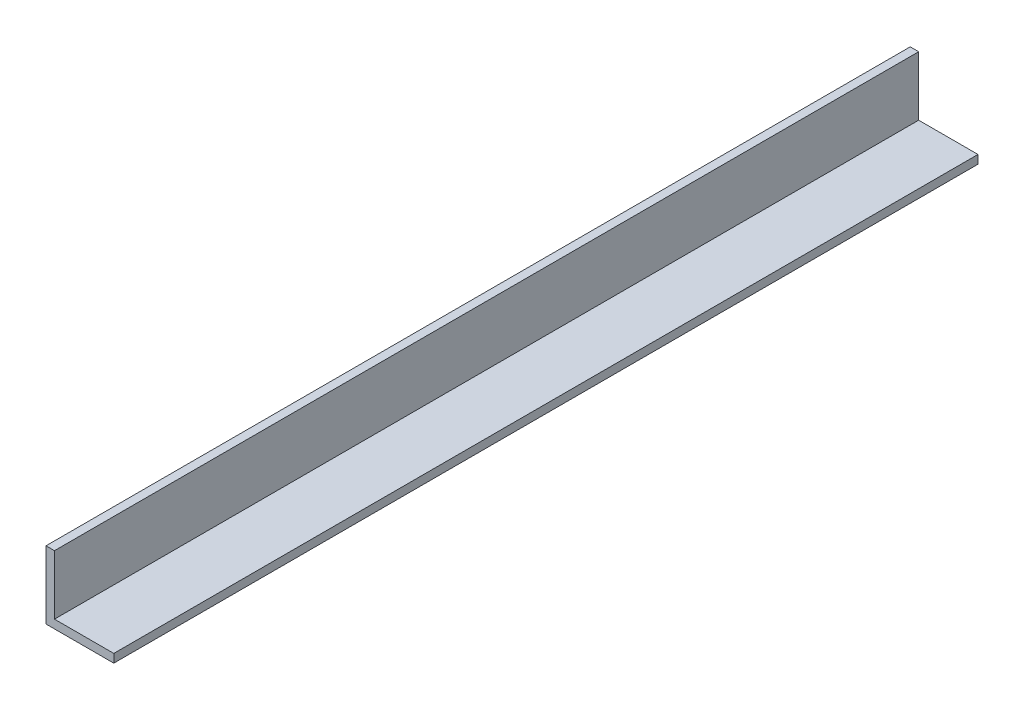
SolidWorks part; units mm, degrees
material "1060 Alloy"
ref_plane "Front Plane" through (0, 0, 0) normal (0, 0, 1) x (1, 0, 0)
ref_plane "Top Plane" through (0, 0, 0) normal (0, 1, 0) x (1, 0, 0)
ref_plane "Right Plane" through (0, 0, 0) normal (1, 0, 0) x (0, 0, -1)
sketch "Sketch1" plane through (0, 0, 0) normal (0, 0, 1) x (1, 0, 0)
  line L1 (0, 0) -> (25.4, 0)
  line L2 (0, 0) -> (0, 25.4)
  line L3 (0, 25.4) -> (3.175, 25.4)
  line L4 (25.4, 0) -> (25.4, 3.175)
  line L7 (25.4, 3.175) -> (3.175, 3.175)
  line L8 (3.175, 25.4) -> (3.175, 3.175)
  dimension "D1" = 25.4
  dimension "D2" = 25.4
  dimension "D3" = 3.175
extrude "Boss-Extrude1" add sketch "Sketch1" along normal blind 323.85
